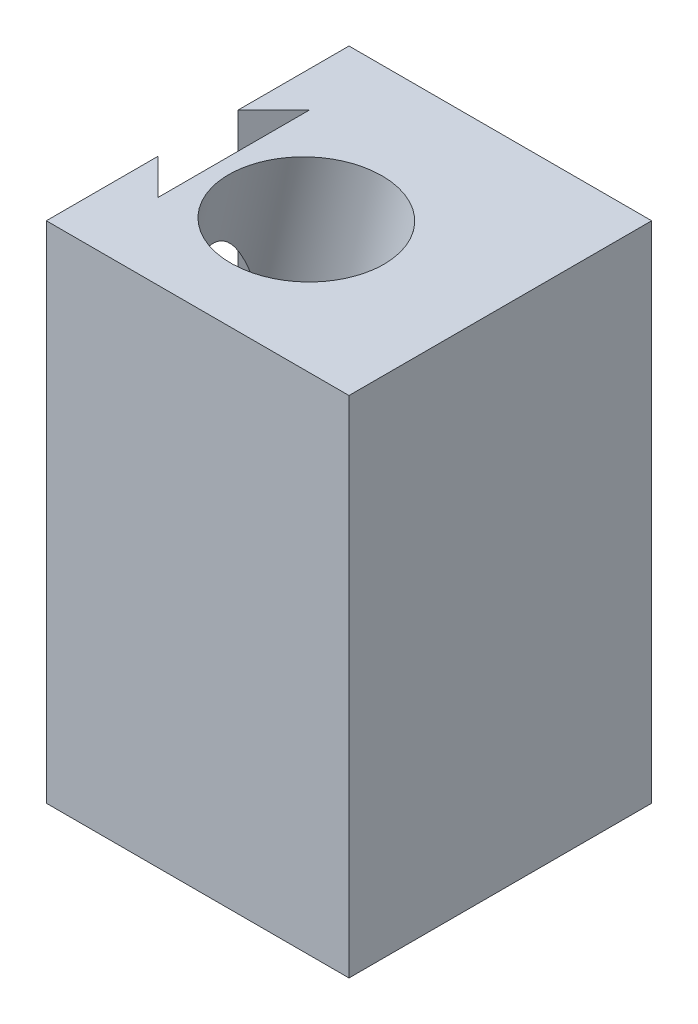
SolidWorks part; units mm, degrees
ref_plane "Front Plane" through (0, 0, 0) normal (0, 0, 1) x (1, 0, 0)
ref_plane "Top Plane" through (0, 0, 0) normal (0, 1, 0) x (1, 0, 0)
ref_plane "Right Plane" through (0, 0, 0) normal (1, 0, 0) x (0, 0, -1)
sketch "Sketch2" plane through (0, 0, 0) normal (0, 1, 0) x (1, 0, 0)
  line L0 (3.5355, 22.5355) -> (3.5355, 7.5355)
  line L1 (0, 0) -> (30, 0)
  line L2 (0, 0) -> (0, 11.0711)
  line L3 (0, 30) -> (30, 30)
  line L4 (30, 0) -> (30, 30)
  line L5 (3.5355, 22.5355) -> (0, 19)
  line L6 (3.5355, 7.5355) -> (0, 11.0711)
  line L7 (0, 19) -> (0, 30)
  dimension "D1" = 30
  dimension "D2" = 30
  dimension "D3" = 15
  dimension "D4" = 5
  dimension "D5" = 5
  dimension "D7" = 135
  dimension "D9" = 11
extrude "Boss-Extrude1" add sketch "Sketch2" along normal blind 50 contours L5 L7 L3 L4 L1 L2 L6 L0
sketch "Sketch3" plane through (0, 50, 0) normal (0, 1, 0) x (1, 0, 0)
  line L0 (0, 30) -> (30, 30) construction
  line L1 (3.5355, 22.5355) -> (3.5355, 7.5355) construction
  circle A0 centre (9.5355, 17) radius 7.5
  dimension "D1" = 15
  dimension "D2" = 13
  dimension "D3" = 6
ref_plane "Plane4" through (12.4774, 54.0454, 0) normal (0.225, 0.9744, 0) x (0, 0, -1)
sketch "Sketch4" plane through (12.4774, 54.0454, 0) normal (0.225, 0.9744, 0) x (0, 0, -1)
  line L0 (30, 11.2476) -> (30, -17.9835) construction
  line L1 (22.5355, 7.8026) -> (7.5355, 7.8026) construction
  circle A0 centre (13, -1.1974) radius 7.5
  dimension "D2" = 15
  dimension "D1" = 17
  dimension "D3" = 9
extrude "Cut-Extrude1" cut sketch "Sketch4" against normal blind 30
sketch "Sketch5" plane through (5.7288, 24.8143, 0) normal (0.225, 0.9744, 0) x (0.9744, -0.225, 0)
  circle A0 centre (1.1974, 13) radius 4.5
  circle A1 centre (1.1974, 13) radius 7.5 construction
  dimension "D2" = 9
  dimension "D1" = 0
extrude "Cut-Extrude2" cut sketch "Sketch5" against normal through all
